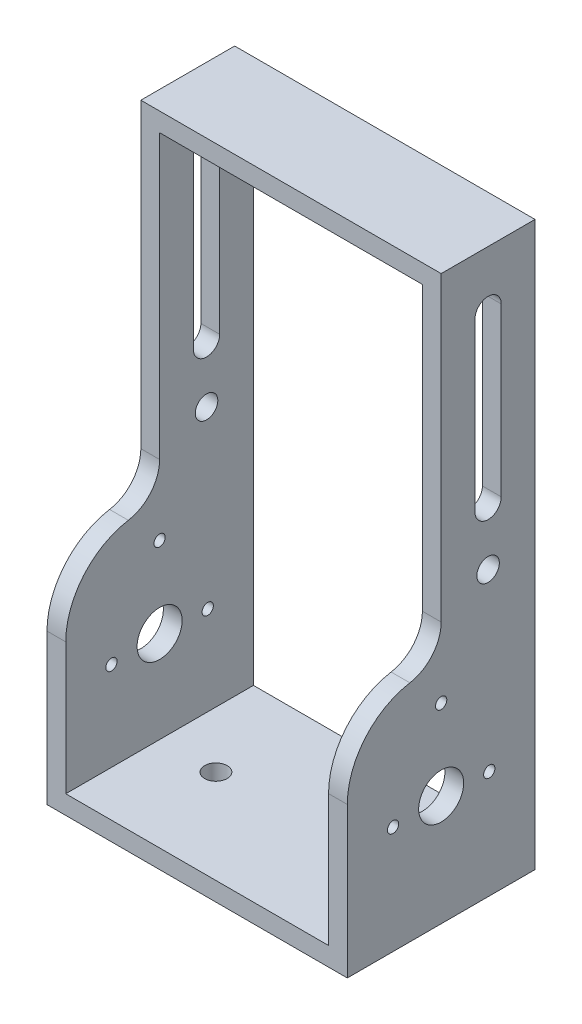
SolidWorks part; units mm, degrees
ref_plane "Front Plane" through (0, 0, 0) normal (0, 0, 1) x (1, 0, 0)
ref_plane "Top Plane" through (0, 0, 0) normal (0, 1, 0) x (1, 0, 0)
ref_plane "Right Plane" through (0, 0, 0) normal (1, 0, 0) x (0, 0, -1)
sketch "Sketch1" plane through (0, 0, 0) normal (0, 0, 1) x (1, 0, 0)
  line L1 (-35, 70) -> (35, 70)
  line L2 (-35, 70) -> (-35, -70)
  line L3 (-35, -70) -> (35, -70)
  line L4 (35, 70) -> (35, -70)
  line L5 (-35, 70) -> (35, -70) construction
  line L6 (-35, -70) -> (35, 70) construction
  point P0 (0, 0)
  dimension "D1" = 70
  dimension "D2" = 140
extrude "Extrude-Thin1" add sketch "Sketch1" along normal mid plane 50 thin thin type one direction wall 5
sketch "Sketch2" plane through (40, 0, 0) normal (1, 0, 0) x (0, 0, -1)
  line L1 (-25, -75) -> (-25, 75) construction
  line L2 (-25, -15.3843) -> (-10, -15.3843)
  line L3 (0, -5.3843) -> (0, 75)
  line L4 (-25, 75) -> (25, 75) construction
  line L5 (0, 75) -> (-25, 75)
  line L6 (-25, 75) -> (-25, -15.3843)
  arc A0 (-10, -15.3843) -> (0, -5.3843) centre (-10, -5.3843) ccw
  dimension "D1" = 10
extrude "Cut-Extrude1" cut sketch "Sketch2" against normal through all both and the other way through all
fillet "Fillet1" radius 20 2 edges at (-37.5, -15.3843, 25) (37.5, -15.3843, 25)
sketch "Sketch3" plane through (40, 0, 0) normal (1, 0, 0) x (0, 0, -1)
  line L0 (12.5, 75) -> (12.5, -75) construction
  line L1 (0, 75) -> (25, 75) construction
  line L2 (-25, -75) -> (25, -75) construction
  line L3 (12.5, 60) -> (12.5, 15.5) construction
  line L4 (16, 60) -> (16, 15.5)
  line L5 (9, 60) -> (9, 15.5)
  line L6 (0, -38.8708) -> (0, -53.6715) construction
  line L7 (0, -38.8708) -> (12.8178, -46.2712) construction
  line L8 (0, -38.8708) -> (-12.8178, -46.2712) construction
  line L9 (0, -38.8708) -> (0, -24.0701) construction
  line L10 (0, -38.8708) -> (25, -38.8708) construction
  line L11 (25, -75) -> (25, 75) construction
  arc A0 (16, 60) -> (9, 60) centre (12.5, 60) ccw
  arc A1 (9, 15.5) -> (16, 15.5) centre (12.5, 15.5) ccw
  circle A3 centre (12.5, 0.5) radius 3
  circle A4 centre (12.5, 0.5) radius 10 construction
  circle A6 centre (0, -38.8708) radius 18.5 construction
  circle A7 centre (0, -24.0701) radius 1.5
  circle A8 centre (12.8178, -46.2712) radius 1.5
  circle A9 centre (0, -45.5238) radius 6
  circle A10 centre (0, -38.8708) radius 6.653 construction
  circle A11 centre (-12.8178, -46.2712) radius 1.5
  point P8 (12.5, 37.75)
  point P13 (-10, -5.3843)
  point P18 (12.5, 10.5)
  point P22 (12.8178, -46.2712)
  point P24 (-12.8178, -46.2712)
  point P27 (0, -24.0701)
  point P37 (0, -45.5238)
  point P38 (0, -45.5238)
  point P39 (0, -20.3708)
  dimension "D2" = 15
  dimension "D3" = 25
  dimension "D4" = 6
  dimension "D5" = 20
  dimension "D12" = 37
  dimension "D13" = 3
  dimension "D15" = 12
  dimension "D1" = 7
  dimension "D7" = 15
  dimension "D8" = 85.5
  dimension "D9" = 14.8007
  dimension "D10" = 120
  dimension "D11" = 120
  dimension "D14" = 6.653
extrude "Cut-Extrude2" cut sketch "Sketch3" against normal through all both and the other way through all
sketch "Sketch5" plane through (0, 70, 0) normal (0, -1, 0) x (1, 0, 0)
  circle A0 centre (0, -12.5) radius 1.5
  dimension "D1" = 3
extrude "Boss-Extrude1" add sketch "Sketch5" along normal blind 4
sketch "Sketch6" plane through (0, -70, 0) normal (0, 1, 0) x (1, 0, 0)
  line L0 (0, -25) -> (0, 25) construction
  line L1 (-35, -25) -> (35, -25) construction
  line L2 (-35, 25) -> (35, 25) construction
  line L3 (-40, 0) -> (40, 0) construction
  circle A0 centre (20, 0) radius 3
  circle A1 centre (-20, 0) radius 3
  dimension "D1" = 6
  dimension "D2" = 20
extrude "Cut-Extrude3" cut sketch "Sketch6" against normal blind 10
